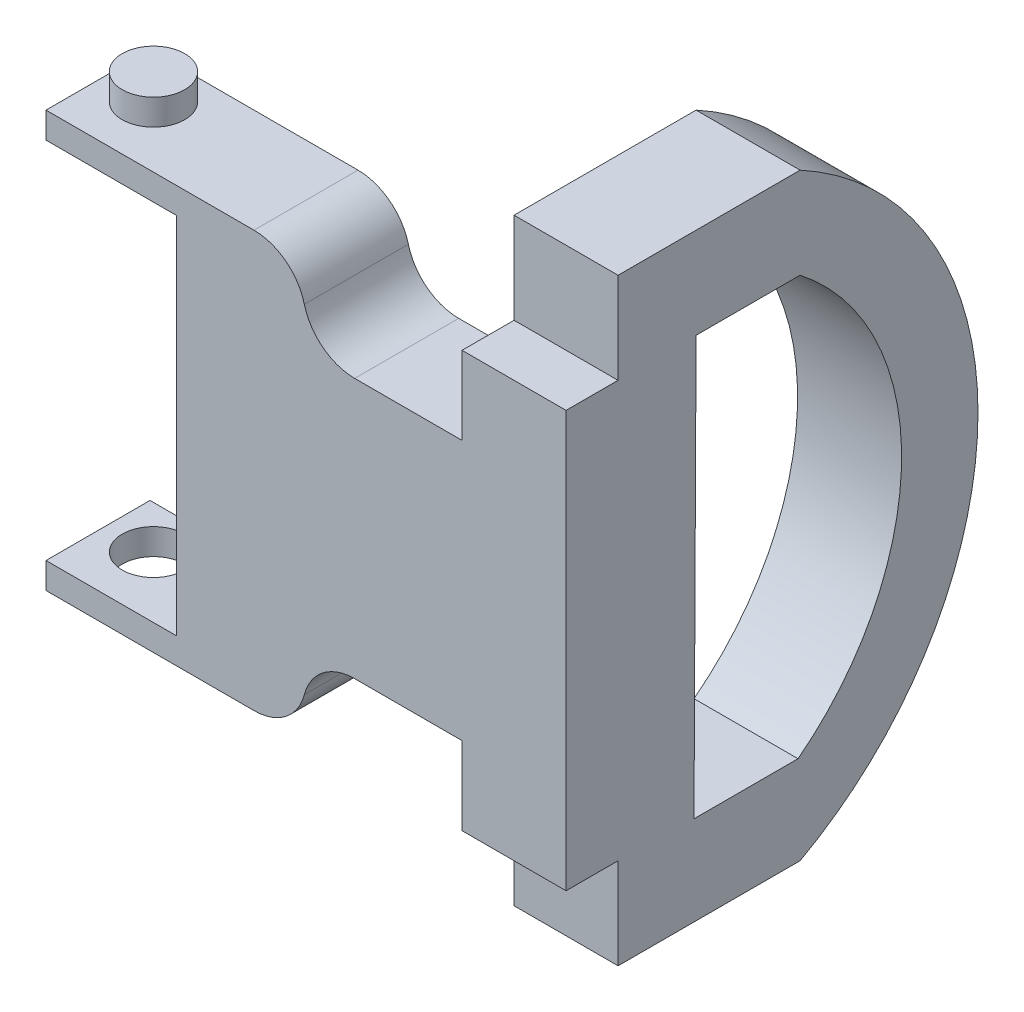
SolidWorks part; units mm, degrees
ref_plane "Front Plane" through (0, 0, 0) normal (0, 0, 1) x (1, 0, 0)
ref_plane "Top Plane" through (0, 0, 0) normal (0, 1, 0) x (1, 0, 0)
ref_plane "Right Plane" through (0, 0, 0) normal (1, 0, 0) x (0, 0, -1)
sketch "Sketch1" plane through (0, 0, 0) normal (1, 0, 0) x (0, 0, -1)
  line L6 (0, -17.661) -> (0, -97.661)
  line L8 (10, -17.661) -> (0, -17.661)
  line L9 (10, -0.161) -> (10, -17.661)
  line L10 (10, -115.161) -> (45, -115.161)
  line L11 (10, -115.161) -> (10, -97.661)
  line L12 (10, -97.661) -> (0, -97.661)
  line L13 (10, -0.161) -> (45, -0.161)
  line L15 (45, -97.661) -> (25, -97.661)
  line L17 (45, -17.661) -> (25, -17.661)
  line L18 (25, -17.661) -> (25, -97.661)
  arc A3 (45, -0.161) -> (45, -115.161) centre (13.7777, -57.661) cw
  arc A4 (45, -97.661) -> (45, -17.661) centre (13.7777, -57.661) ccw
extrude "Boss-Extrude3" add sketch "Sketch1" along normal blind 20 contours L6 L12 L11 L10 A3 L13 L9 L8
sketch "Sketch3" plane through (20, 0, 0) normal (1, 0, 0) x (0, 0, -1)
  line L0 (45, -17.661) -> (25, -17.661)
  line L1 (44.5991, -97.9707) -> (24.5991, -97.9707)
  line L2 (25, -17.661) -> (24.5991, -97.9707)
  arc A2 (45, -17.661) -> (44.5991, -97.9707) centre (13.7777, -57.661) cw
extrude "Cut-Extrude3" cut sketch "Sketch3" against normal blind 20
sketch "Sketch4" plane through (0, 0, 0) normal (0, 0, 1) x (1, 0, 0)
  line L0 (0, -17.661) -> (0, -32.661)
  line L1 (0, -17.661) -> (0, -97.661) construction
  line L2 (0, -32.661) -> (-20.64, -32.661)
  line L3 (0, -97.661) -> (0, -82.661)
  line L4 (-20.64, -82.661) -> (0, -82.661)
  line L9 (-80, -17.661) -> (-79.9336, -32.6609)
  line L10 (-79.9336, -32.6609) -> (-54.9336, -32.6609)
  line L12 (-54.9336, -82.661) -> (-80, -82.661)
  line L13 (-80, -82.661) -> (-80, -97.661)
  line L15 (-54.9336, -82.661) -> (-54.9336, -32.6609)
  line L18 (-30.64, -22.661) -> (-40.64, -22.661)
  line L21 (-30.64, -92.661) -> (-40.64, -92.661)
  line L22 (-40.64, -22.661) -> (-40.64, -17.661)
  line L23 (-40.64, -92.661) -> (-40.64, -97.661)
  line L24 (-80, -17.661) -> (-40.64, -17.661)
  line L25 (-40.64, -97.661) -> (-80, -97.661)
  line L30 (0, -17.661) -> (0, -97.661)
  line L31 (0, -97.661) -> (20, -97.661)
  line L32 (20, -97.661) -> (20, -17.661)
  line L33 (20, -17.661) -> (0, -17.661)
  line L35 (0, -97.661) -> (20, -97.661)
  line L36 (20, -97.661) -> (20, -17.661)
  line L37 (20, -17.661) -> (0, -17.661)
  arc A0 (-20.64, -32.661) -> (-30.64, -22.661) centre (-20.64, -22.661) cw
  arc A3 (-20.64, -82.661) -> (-30.64, -92.661) centre (-20.64, -92.661) ccw
  dimension "D1" = 0
extrude "Boss-Extrude4" add sketch "Sketch4" against normal blind 20 contours L24 L22 L18 A0 L2 L0 L37 L36 L35 L3 L4 A3 L21 L23 L25 L13 L12 L15 L10 L9
sketch "Sketch5" plane through (0, 0, 0) normal (0, 0, 1) x (1, 0, 0)
  line L0 (-40.64, -22.661) -> (-40.64, -17.661)
  line L1 (-30.64, -92.661) -> (-30.64, -97.661)
extrude "Extrude-Thin1" add sketch "Sketch5" against normal blind 20 thin
fillet "Fillet1" radius 10 2 edges at (-30.64, -22.661, -10) (-30.64, -17.661, -10)
fillet "Fillet2" radius 10 2 edges at (-30.64, -97.661, -10) (-30.64, -92.661, -10)
sketch "Sketch6" plane through (0, -17.661, 0) normal (0, 1, 0) x (1, 0, 0)
  circle A0 centre (-71.072, 11.7357) radius 6
extrude "Cut-Extrude5" cut sketch "Sketch6" against normal through all
sketch "Sketch7" plane through (0, 0, 0) normal (0, 0, 1) x (1, 0, 0)
  line L0 (-80, -17.661) -> (-79.9336, -32.6609) construction
  line L1 (-79.9613, -26.4109) -> (-54.9336, -26.4109)
  line L2 (-79.9613, -26.4109) -> (-79.9613, -32.6609)
  line L3 (-79.9613, -32.6609) -> (-54.9336, -32.6609)
  line L4 (-54.9336, -26.4109) -> (-54.9336, -32.6609)
  line L5 (-80, -82.661) -> (-80, -97.661) construction
  line L6 (-80, -88.911) -> (-54.9336, -88.911)
  line L7 (-80, -88.911) -> (-80, -82.661)
  line L8 (-80, -82.661) -> (-54.9336, -82.661)
  line L9 (-54.9336, -88.911) -> (-54.9336, -82.661)
  dimension "D1" = 6.25
  dimension "D2" = 6.25
extrude "Cut-Extrude6" cut sketch "Sketch7" against normal through all
sketch "Sketch8" plane through (0, -17.661, 0) normal (0, 1, 0) x (1, 0, 0)
  circle A0 centre (-71.072, 11.7357) radius 6.0111
  dimension "D1" = 12.0222
extrude "Boss-Extrude6" add sketch "Sketch8" along normal blind 5
sketch "Sketch9" plane through (0, 0, 0) normal (0, 0, 1) x (1, 0, 0)
  line L1 (-83.496, -22.661) -> (-54.9336, -22.661)
  line L2 (-83.496, -22.661) -> (-84.9059, -92.661)
  line L3 (-84.9059, -92.661) -> (-54.9336, -92.661)
  line L4 (-54.9336, -22.661) -> (-54.9336, -92.661)
  line L5 (-54.9336, -88.911) -> (-54.9336, -26.4109) construction
  dimension "D1" = 5
  dimension "D2" = 5
extrude "Cut-Extrude9" cut sketch "Sketch9" against normal blind 35
